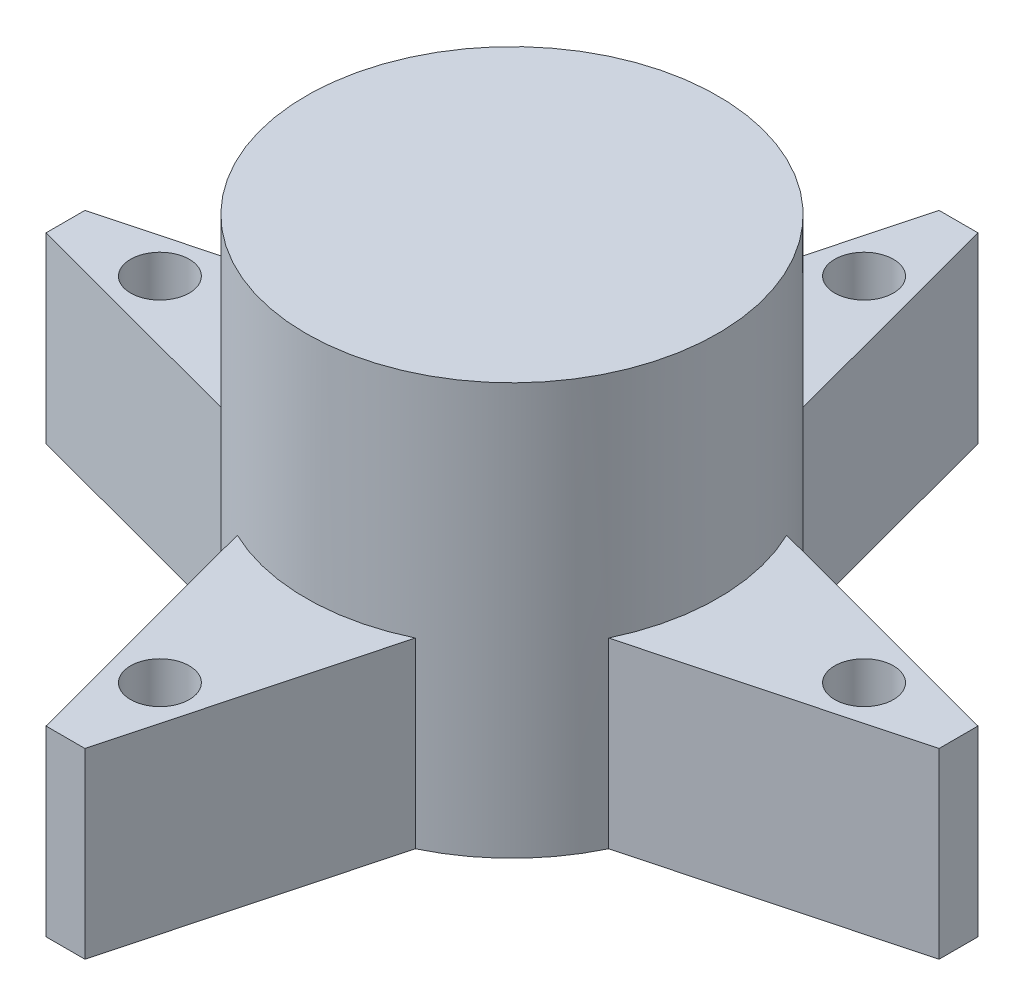
SolidWorks part; units mm, degrees
ref_plane "Front Plane" through (0, 0, 0) normal (0, 0, 1) x (1, 0, 0)
ref_plane "Top Plane" through (0, 0, 0) normal (0, 1, 0) x (1, 0, 0)
ref_plane "Right Plane" through (0, 0, 0) normal (1, 0, 0) x (0, 0, -1)
sketch "Sketch1" plane through (0, 0, 0) normal (0, 1, 0) x (1, 0, 0)
  circle A0 centre (0, 0) radius 7.895
  dimension "D1" = 15.79
extrude "Boss-Extrude1" add sketch "Sketch1" along normal blind 15.79
sketch "Sketch2" plane through (0, 0, 0) normal (0, 1, 0) x (1, 0, 0)
  line L0 (0, -10.5708) -> (0, 10.9706) construction
  line L1 (11.3925, 0) -> (-11.1704, 0) construction
  line L2 (7.1189, -3.4135) -> (17.1218, -0.7462)
  line L3 (17.1218, 0.7462) -> (7.1189, 3.4135)
  line L4 (17.1218, -0.7462) -> (17.1218, 0.7462)
  line L5 (-3.4135, -7.1189) -> (-0.7462, -17.1218)
  line L6 (0.7462, -17.1218) -> (3.4135, -7.1189)
  line L7 (-0.7462, -17.1218) -> (0.7462, -17.1218)
  line L8 (-7.1189, 3.4135) -> (-17.1218, 0.7462)
  line L9 (-17.1218, -0.7462) -> (-7.1189, -3.4135)
  line L10 (-17.1218, 0.7462) -> (-17.1218, -0.7462)
  line L11 (3.4135, 7.1189) -> (0.7462, 17.1218)
  line L12 (-0.7462, 17.1218) -> (-3.4135, 7.1189)
  line L13 (0.7462, 17.1218) -> (-0.7462, 17.1218)
  line L14 (-7.1189, -3.4135) -> (-3.4135, -7.1189)
  line L15 (3.4135, -7.1189) -> (7.1189, -3.4135)
  line L16 (7.1189, 3.4135) -> (3.4135, 7.1189)
  line L17 (-3.4135, 7.1189) -> (-7.1189, 3.4135)
  circle A0 centre (13.5, 0) radius 1.125
  circle A1 centre (0, 0) radius 7.895 construction
  circle A2 centre (0, -13.5) radius 1.125
  circle A3 centre (-13.5, 0) radius 1.125
  circle A4 centre (0, 13.5) radius 1.125
  point P34 (0, 0)
  dimension "D2" = 2.25
  dimension "D1" = 13.5
  dimension "D3" = 4
extrude "Boss-Extrude2" add sketch "Sketch2" along normal blind 7 contours L6 L15 L2 L4 L3 L16 L11 L13 L12 L17 L8 L10 L9 L14 L5 L7
